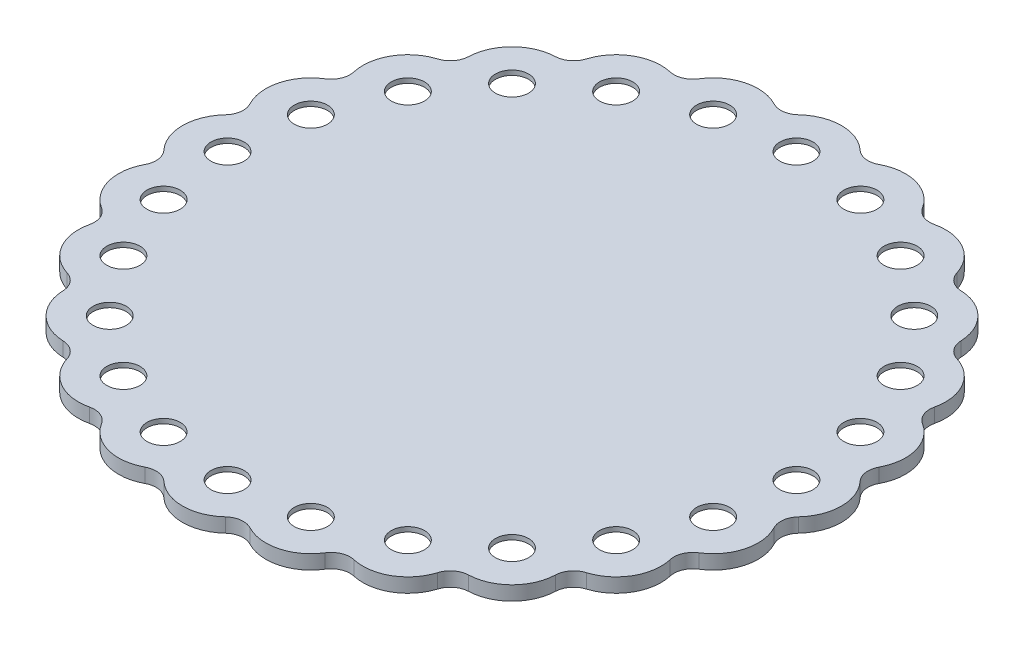
SolidWorks part; units mm, degrees
material "3.1355 (EN-AW 2024)"
ref_plane "Front" through (0, 0, 0) normal (0, 0, 1) x (1, 0, 0)
ref_plane "Top" through (0, 0, 0) normal (0, 1, 0) x (1, 0, 0)
ref_plane "Right" through (0, 0, 0) normal (1, 0, 0) x (0, 0, -1)
sketch "Эскиз1" plane through (0, 0, 0) normal (0, 1, 0) x (1, 0, 0)
  circle A0 centre (0, 0) radius 60 construction
  circle A1 centre (0, 60) radius 3.5
  circle A2 centre (15.5291, 57.9555) radius 3.5
  circle A3 centre (30, 51.9615) radius 3.5
  circle A4 centre (42.4264, 42.4264) radius 3.5
  circle A5 centre (51.9615, 30) radius 3.5
  circle A6 centre (57.9555, 15.5291) radius 3.5
  circle A7 centre (60, 0) radius 3.5
  circle A8 centre (57.9555, -15.5291) radius 3.5
  circle A9 centre (51.9615, -30) radius 3.5
  circle A10 centre (42.4264, -42.4264) radius 3.5
  circle A11 centre (30, -51.9615) radius 3.5
  circle A12 centre (15.5291, -57.9555) radius 3.5
  circle A13 centre (0, -60) radius 3.5
  circle A14 centre (-15.5291, -57.9555) radius 3.5
  circle A15 centre (-30, -51.9615) radius 3.5
  circle A16 centre (-42.4264, -42.4264) radius 3.5
  circle A17 centre (-51.9615, -30) radius 3.5
  circle A18 centre (-57.9555, -15.5291) radius 3.5
  circle A19 centre (-60, 0) radius 3.5
  circle A20 centre (-57.9555, 15.5291) radius 3.5
  circle A21 centre (-51.9615, 30) radius 3.5
  circle A22 centre (-42.4264, 42.4264) radius 3.5
  circle A23 centre (-30, 51.9615) radius 3.5
  circle A24 centre (-15.5291, 57.9555) radius 3.5
  point P54 (0, 0)
  dimension "D1" = 7
  dimension "D2" = 24
  dimension "D3" = 120
sketch "Эскиз2" plane through (0, 0, 0) normal (0, 1, 0) x (1, 0, 0)
  line L0 (0, 0) -> (0, 60) construction
  circle A0 centre (0, 0) radius 60 construction
  circle A2 centre (0, 60) radius 6.5
  circle A3 centre (15.5291, 57.9555) radius 6.5
  circle A4 centre (30, 51.9615) radius 6.5
  circle A5 centre (42.4264, 42.4264) radius 6.5
  circle A6 centre (51.9615, 30) radius 6.5
  circle A7 centre (57.9555, 15.5291) radius 6.5
  circle A8 centre (60, 0) radius 6.5
  circle A9 centre (57.9555, -15.5291) radius 6.5
  circle A10 centre (51.9615, -30) radius 6.5
  circle A11 centre (42.4264, -42.4264) radius 6.5
  circle A12 centre (30, -51.9615) radius 6.5
  circle A13 centre (15.5291, -57.9555) radius 6.5
  circle A14 centre (0, -60) radius 6.5
  circle A15 centre (-15.5291, -57.9555) radius 6.5
  circle A16 centre (-30, -51.9615) radius 6.5
  circle A17 centre (-42.4264, -42.4264) radius 6.5
  circle A18 centre (-51.9615, -30) radius 6.5
  circle A19 centre (-57.9555, -15.5291) radius 6.5
  circle A20 centre (-60, 0) radius 6.5
  circle A21 centre (-57.9555, 15.5291) radius 6.5
  circle A22 centre (-51.9615, 30) radius 6.5
  circle A23 centre (-42.4264, 42.4264) radius 6.5
  circle A24 centre (-30, 51.9615) radius 6.5
  circle A25 centre (-15.5291, 57.9555) radius 6.5
  dimension "D1" = 13
  dimension "D2" = 120
  dimension "D4" = 60
  dimension "D3" = 24
sketch "Эскиз3" plane through (0, 0, 0) normal (0, 1, 0) x (1, 0, 0)
  line L0 (0, 0) -> (0, 60) construction
  line L1 (0, 0) -> (0, 60) construction
  arc A0 (-6.474, 66.9525) -> (6.474, 66.9525) centre (0, 60) cw
  arc A1 (11.0752, 66.3468) -> (23.582, 62.9956) centre (15.5291, 57.9555) cw
  arc A2 (27.8696, 61.2196) -> (39.0829, 54.7456) centre (30, 51.9615) cw
  arc A3 (42.7648, 51.9204) -> (51.9204, 42.7648) centre (42.4264, 42.4264) cw
  arc A4 (54.7456, 39.0829) -> (61.2196, 27.8696) centre (51.9615, 30) cw
  arc A5 (62.9956, 23.582) -> (66.3468, 11.0752) centre (57.9555, 15.5291) cw
  arc A6 (66.9525, 6.474) -> (66.9525, -6.474) centre (60, 0) cw
  arc A7 (66.3468, -11.0752) -> (62.9956, -23.582) centre (57.9555, -15.5291) cw
  arc A8 (61.2196, -27.8696) -> (54.7456, -39.0829) centre (51.9615, -30) cw
  arc A9 (51.9204, -42.7648) -> (42.7648, -51.9204) centre (42.4264, -42.4264) cw
  arc A10 (39.0829, -54.7456) -> (27.8696, -61.2196) centre (30, -51.9615) cw
  arc A11 (23.582, -62.9956) -> (11.0752, -66.3468) centre (15.5291, -57.9555) cw
  arc A12 (6.474, -66.9525) -> (-6.474, -66.9525) centre (0, -60) cw
  arc A13 (-11.0752, -66.3468) -> (-23.582, -62.9956) centre (-15.5291, -57.9555) cw
  arc A14 (-27.8696, -61.2196) -> (-39.0829, -54.7456) centre (-30, -51.9615) cw
  arc A15 (-42.7648, -51.9204) -> (-51.9204, -42.7648) centre (-42.4264, -42.4264) cw
  arc A16 (-54.7456, -39.0829) -> (-61.2196, -27.8696) centre (-51.9615, -30) cw
  arc A17 (-62.9956, -23.582) -> (-66.3468, -11.0752) centre (-57.9555, -15.5291) cw
  arc A18 (-66.9525, -6.474) -> (-66.9525, 6.474) centre (-60, 0) cw
  arc A19 (-66.3468, 11.0752) -> (-62.9956, 23.582) centre (-57.9555, 15.5291) cw
  arc A20 (-61.2196, 27.8696) -> (-54.7456, 39.0829) centre (-51.9615, 30) cw
  arc A21 (-51.9204, 42.7648) -> (-42.7648, 51.9204) centre (-42.4264, 42.4264) cw
  arc A22 (-39.0829, 54.7456) -> (-27.8696, 61.2196) centre (-30, 51.9615) cw
  arc A23 (-23.582, 62.9956) -> (-11.0752, 66.3468) centre (-15.5291, 57.9555) cw
  arc A24 (11.0752, 66.3468) -> (6.474, 66.9525) centre (9.1999, 69.8799) cw
  arc A25 (-27.8696, -61.2196) -> (-23.582, -62.9956) centre (-26.9726, -65.1177) cw
  arc A26 (-11.0752, -66.3468) -> (-6.474, -66.9525) centre (-9.1999, -69.8799) cw
  arc A27 (6.474, -66.9525) -> (11.0752, -66.3468) centre (9.1999, -69.8799) cw
  arc A28 (23.582, -62.9956) -> (27.8696, -61.2196) centre (26.9726, -65.1177) cw
  arc A29 (39.0829, -54.7456) -> (42.7648, -51.9204) centre (42.9073, -55.9178) cw
  arc A30 (51.9204, -42.7648) -> (54.7456, -39.0829) centre (55.9178, -42.9073) cw
  arc A31 (61.2196, -27.8696) -> (62.9956, -23.582) centre (65.1177, -26.9726) cw
  arc A32 (66.3468, -11.0752) -> (66.9525, -6.474) centre (69.8799, -9.1999) cw
  arc A33 (66.9525, 6.474) -> (66.3468, 11.0752) centre (69.8799, 9.1999) cw
  arc A34 (62.9956, 23.582) -> (61.2196, 27.8696) centre (65.1177, 26.9726) cw
  arc A35 (54.7456, 39.0829) -> (51.9204, 42.7648) centre (55.9178, 42.9073) cw
  arc A36 (39.0829, 54.7456) -> (42.7648, 51.9204) centre (42.9073, 55.9178) ccw
  arc A37 (27.8696, 61.2196) -> (23.582, 62.9956) centre (26.9726, 65.1177) cw
  arc A38 (-42.7648, -51.9204) -> (-39.0829, -54.7456) centre (-42.9073, -55.9178) cw
  arc A39 (-6.474, 66.9525) -> (-11.0752, 66.3468) centre (-9.1999, 69.8799) cw
  arc A40 (-23.582, 62.9956) -> (-27.8696, 61.2196) centre (-26.9726, 65.1177) cw
  arc A41 (-39.0829, 54.7456) -> (-42.7648, 51.9204) centre (-42.9073, 55.9178) cw
  arc A42 (-51.9204, 42.7648) -> (-54.7456, 39.0829) centre (-55.9178, 42.9073) cw
  arc A43 (-61.2196, 27.8696) -> (-62.9956, 23.582) centre (-65.1177, 26.9726) cw
  arc A44 (-66.3468, 11.0752) -> (-66.9525, 6.474) centre (-69.8799, 9.1999) cw
  arc A45 (-66.9525, -6.474) -> (-66.3468, -11.0752) centre (-69.8799, -9.1999) cw
  arc A46 (-62.9956, -23.582) -> (-61.2196, -27.8696) centre (-65.1177, -26.9726) cw
  arc A47 (-54.7456, -39.0829) -> (-51.9204, -42.7648) centre (-55.9178, -42.9073) cw
  dimension "D3" = 9.5
  dimension "D4" = 4
  dimension "D5" = 4
  dimension "D6" = 4
  dimension "D7" = 4
  dimension "D2" = 60
  dimension "D1" = 24
extrude "Бобышка-Вытянуть2" add sketch "Эскиз3" along normal blind 3
extrude "Вырез-Вытянуть2" cut sketch "Эскиз1" along normal through all
extrude "Вырез-Вытянуть4" cut sketch "Эскиз2" along normal offset from surface (2 mm away) 1 up to face at (-30, 3, -48.4615)
equation "\"D path poles\" = 120"
equation "\"D3@Эскиз1\"=\"D path poles\""
equation "\"D2@Эскиз2\"=\"D path poles\""
equation "\"D2@Эскиз3\"=\"D path poles\"/2"
equation "\"D4@Эскиз2\"=\"D path poles\"/2"
